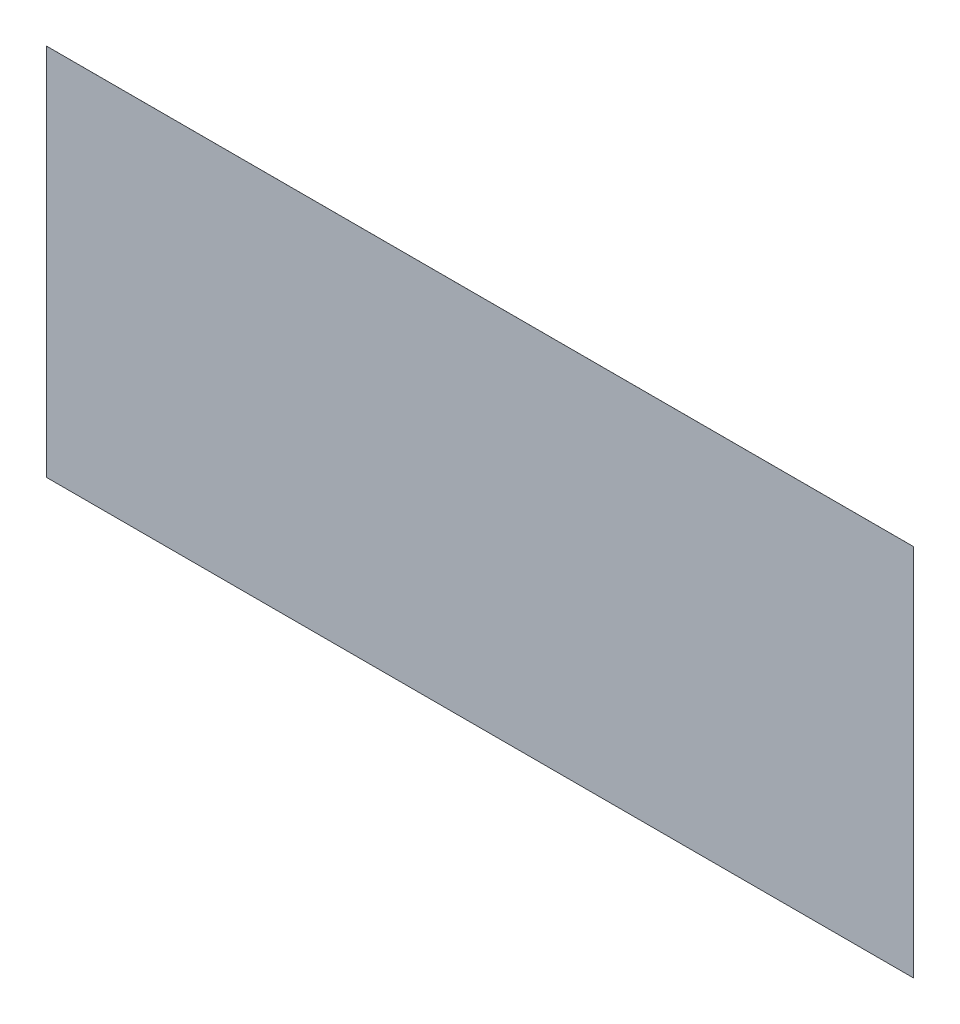
SolidWorks part; units mm, degrees
ref_plane "Front Plane" through (0, 0, 0) normal (0, 0, 1) x (1, 0, 0)
ref_plane "Top Plane" through (0, 0, 0) normal (0, 1, 0) x (1, 0, 0)
ref_plane "Right Plane" through (0, 0, 0) normal (1, 0, 0) x (0, 0, -1)
sketch "Sketch1" plane through (0, 0, 0) normal (0, 0, 1) x (1, 0, 0)
  line L0 (-5.06, -2.475) -> (5.06, -2.475)
  line L1 (5.06, -2.475) -> (5.06, 1.885)
  line L2 (5.06, 1.885) -> (-5.06, 1.885)
  line L3 (-5.06, 1.885) -> (-5.06, -2.475)
extrude "Boss-Extrude1" add sketch "Sketch1" along normal blind 0.0003 from offset 0
